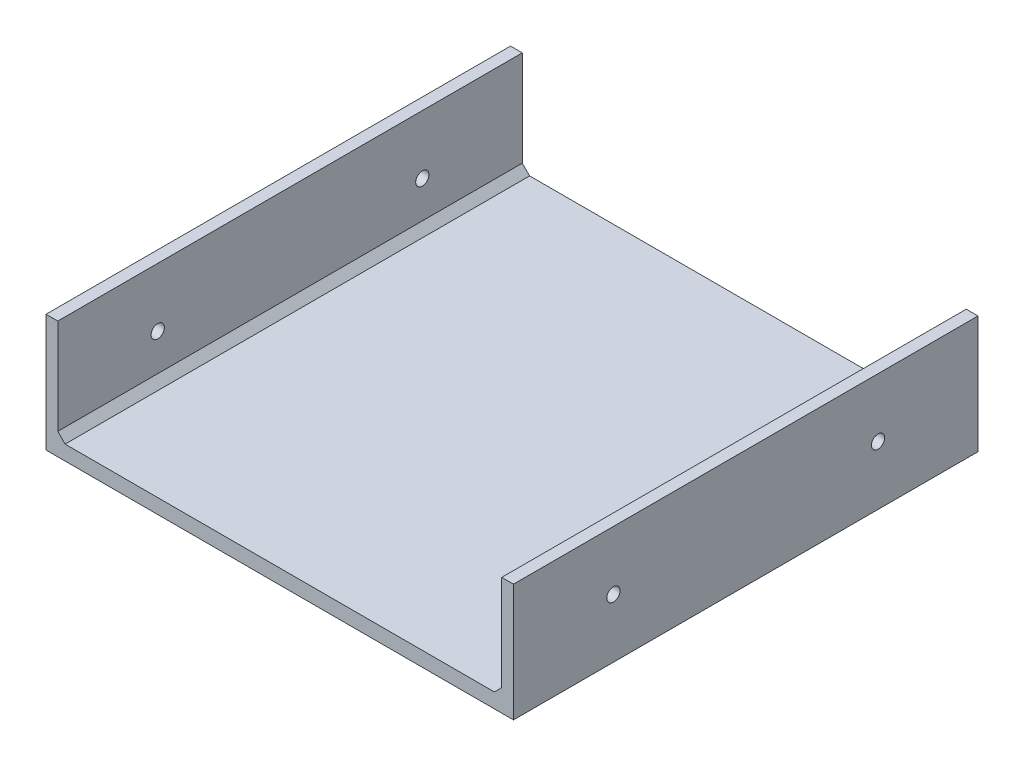
SolidWorks part; units mm, degrees
ref_plane "Front Plane" through (0, 0, 0) normal (0, 0, 1) x (1, 0, 0)
ref_plane "Top Plane" through (0, 0, 0) normal (0, 1, 0) x (1, 0, 0)
ref_plane "Right Plane" through (0, 0, 0) normal (1, 0, 0) x (0, 0, -1)
sketch "Sketch1" plane through (0, 0, 0) normal (0, 1, 0) x (1, 0, 0)
  line L1 (-79.5, 0) -> (79.5, 0)
  line L2 (-79.5, 0) -> (-79.5, -158)
  line L3 (-79.5, -158) -> (79.5, -158)
  line L4 (79.5, 0) -> (79.5, -158)
  point P4 (0, 0)
  dimension "D1" = 159
  dimension "D2" = 158
extrude "Boss-Extrude1" add sketch "Sketch1" along normal blind 5
sketch "Sketch2" plane through (0, 0, 0) normal (0, -1, 0) x (1, 0, 0)
  line L0 (-79.5, 0) -> (-79.5, 158) construction
  line L1 (79.5, 0) -> (-79.5, 0) construction
  line L2 (79.5, 0) -> (79.5, 40) construction
  line L3 (79.5, 40) -> (-79.5, 40) construction
  line L4 (-79.5, 0) -> (-79.5, 40) construction
  line L5 (79.5, 20) -> (0, 20) construction
  line L6 (0, 40) -> (0, 0) construction
  line L7 (0, 20) -> (-79.5, 20) construction
  point P12 (39.75, 20)
  point P14 (-39.75, 20)
  dimension "D1" = 40
hole_wizard "CBORE for M4 SHCS1" [suppressed] positions "Sketch2" profile "Sketch3" counterbore size "M4" standard "ANSI Metric"
sketch "Sketch3" plane through (-18.75, 0, 20) normal (1, 0, 0) x (0, 0, -1)
  line L0 (0, 0) -> (0, 5)
  line L1 (0, 5) -> (2.25, 5)
  line L3 (2.25, 5) -> (2.25, 4)
  line L4 (2.25, 4) -> (4, 4)
  line L5 (4, 4) -> (4, 0)
  line L7 (4, 0) -> (0, 0)
  line L11 (0, -6.35) -> (0, 107.95) construction
  dimension "Thru Hole Dia." = 4.5
  dimension "Thru Hole Depth" = 5
  dimension "C'Bore Dia." = 8
  dimension "C'Bore Depth" = 4
sketch "Sketch4" plane through (0, 5, 0) normal (0, 1, 0) x (1, 0, 0)
  line L13 (79.5, 0) -> (-79.5, 0) construction
  line L15 (79.5, -158) -> (75.5, -158)
  line L16 (79.5, -158) -> (79.5, 0)
  line L17 (79.5, 0) -> (75.5, 0)
  line L18 (75.5, -158) -> (75.5, 0)
  dimension "D1" = 4
extrude "Boss-Extrude2" add sketch "Sketch4" along normal blind 35
sketch "Sketch8" plane through (75.5, 0, 0) normal (-1, 0, 0) x (0, 0, 1)
  line L13 (79, 40) -> (79, 20) construction
  line L14 (0, 40) -> (158, 40) construction
  line L16 (79, 20) -> (34, 20) construction
  point P42 (34, 20)
  point P44 (124, 20)
  dimension "D1" = 20
  dimension "D2" = 90
hole_wizard "M4 Clearance Hole1" positions "Sketch8" profile "Sketch9" hole size "M4" standard "ANSI Metric" end condition through all
sketch "Sketch9" plane through (75.5, 20, 124) normal (0, 1, 0) x (0, 0, 1)
  line L0 (0, 0) -> (0, 4)
  line L1 (0, 4) -> (2.25, 4)
  line L2 (2.25, 4) -> (2.25, 0)
  line L5 (2.25, 0) -> (0, 0)
  line L11 (0, -6.35) -> (0, 107.95) construction
  dimension "Thru Hole Dia." = 4.5
  dimension "Thru Hole Depth" = 4
sketch "Sketch10" plane through (0, 5, 0) normal (0, 1, 0) x (1, 0, 0)
  line L0 (-79.5, 0) -> (-79.5, -158) construction
  line L1 (75.5, 0) -> (-79.5, -158) construction
  circle A0 centre (50.5, -25.4839) radius 10
  dimension "D2" = 20
  dimension "D1" = 130
extrude "Cut-Extrude2" [suppressed] cut sketch "Sketch10" against normal up to next
ref_plane "Plane2" through (0, 0, 0) normal (-1, 0, 0) x (0, 0, 1)
mirror "Mirror2" about plane through (0, 0, 0) normal (-1, 0, 0) of "M4 Clearance Hole1", "Boss-Extrude2"
sketch "Sketch13" plane through (0, 5, 0) normal (0, 1, 0) x (1, 0, 0)
  line L5 (-79.5, 0) -> (-4.5, 0)
  line L6 (-79.5, 0) -> (-79.5, -15)
  line L7 (-79.5, -15) -> (-4.5, -15)
  line L8 (-4.5, 0) -> (-4.5, -15)
  dimension "D3" = 75
  dimension "D4" = 15
extrude "Cut-Extrude4" [suppressed] cut sketch "Sketch13" against normal through all and the other way through all
sketch "Sketch14" [suppressed] plane through (0, 5, 0) normal (0, 1, 0) x (1, 0, 0)
  line L19 (73.75, 0) -> (-4.75, 0)
  line L20 (-4.75, 0) -> (-4.75, -15)
  line L21 (-4.75, -15) -> (-73.75, -15)
  line L22 (-73.75, -15) -> (-73.75, -20)
  line L23 (-73.75, -15) -> (-73.75, -158) construction
  line L24 (-73.75, -20) -> (0.25, -20)
  line L25 (0.25, -20) -> (0.25, -5)
  line L26 (0.25, -5) -> (73.75, -5)
  line L27 (73.75, 0) -> (73.75, -158) construction
  line L28 (73.75, -5) -> (73.75, 0)
  line L29 (73.75, 0) -> (-4.75, 0) construction
  dimension "D1" = 5
  dimension "D2" = 5
  dimension "D3" = 5
extrude "Boss-Extrude4" [suppressed] add sketch "Sketch14" along normal blind 5
fillet "Fillet1" [suppressed] radius 2.5
sketch "Sketch15" [suppressed] plane through (0, 5, 0) normal (0, 1, 0) x (1, 0, 0)
  line L0 (53.75, -24.2516) -> (53.75, -92.815) construction
  line L1 (73.75, -7.5) -> (73.75, -158) construction
  line L3 (-71.25, -158) -> (71.25, -158) construction
  circle A0 centre (53.75, -78) radius 3.05
  circle A1 centre (53.75, -128) radius 3.05
  dimension "D2" = 6.1
  dimension "D3" = 50
  dimension "D1" = 20
  dimension "D4" = 30
extrude "Cut-Extrude5" [suppressed] cut sketch "Sketch15" against normal blind 3.1
pattern_linear "LPattern1" [suppressed] count 2 spacing 30
mirror "Mirror3" [suppressed] about plane through (0, 0, 0) normal (-1, 0, 0)
chamfer "Chamfer1" [suppressed] distance 0.25 angle 45
chamfer "Chamfer2" distance 2.5 angle 45 2 edges at (-75.5, 5, 79) (75.5, 5, 79)
equation "\"D2@Sketch14\"=\"D1@Sketch14\""
equation "\"D3@Sketch14\"=\"D1@Sketch14\""
